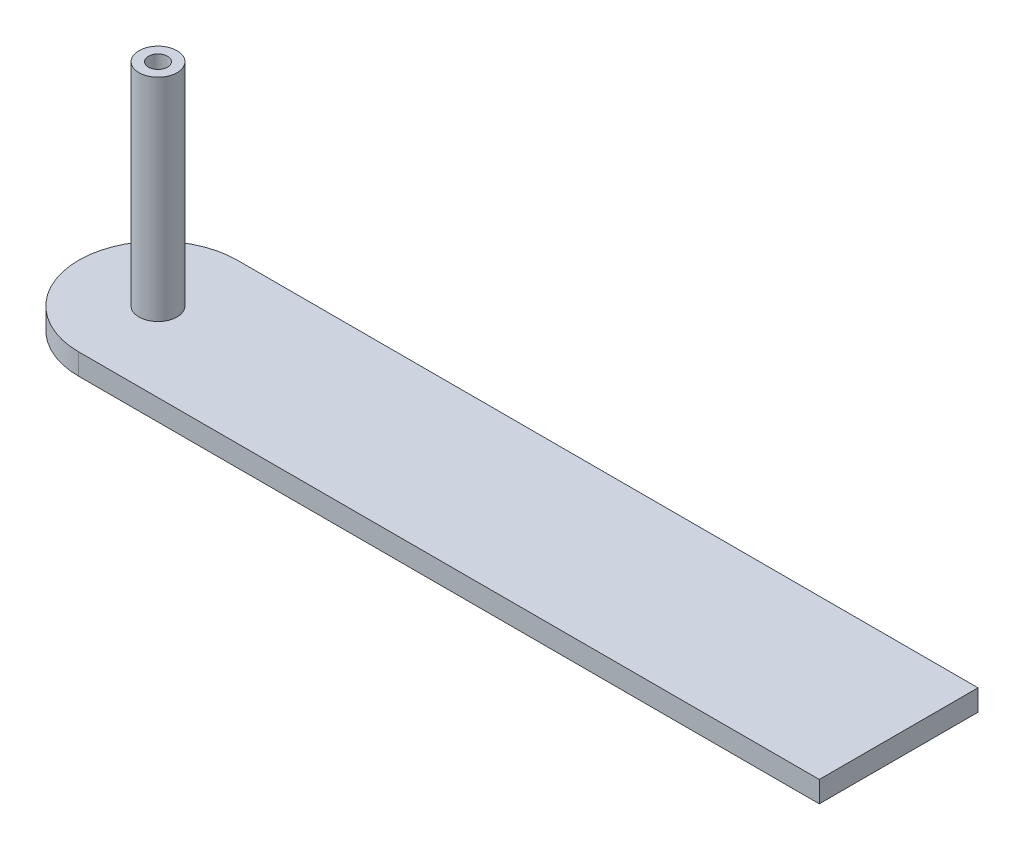
SolidWorks part; units mm, degrees
ref_plane "Front Plane" through (0, 0, 0) normal (0, 0, 1) x (1, 0, 0)
ref_plane "Top Plane" through (0, 0, 0) normal (0, 1, 0) x (1, 0, 0)
ref_plane "Right Plane" through (0, 0, 0) normal (1, 0, 0) x (0, 0, -1)
sketch "Sketch1" plane through (0, 0, 0) normal (0, 1, 0) x (1, 0, 0)
  line L1 (0, 0) -> (70, 0)
  line L2 (0, 0) -> (0, 15)
  line L3 (0, 15) -> (70, 15)
  line L4 (70, 0) -> (70, 15)
  dimension "D1" = 15
  dimension "D2" = 70
extrude "Boss-Extrude1" add sketch "Sketch1" along normal blind 2
sketch "Sketch2" plane through (0, 2, 0) normal (0, 1, 0) x (1, 0, 0)
  line L0 (0, 0) -> (0, 15) construction
  circle A0 centre (0, 7.5) radius 7.5
extrude "Boss-Extrude2" add sketch "Sketch2" along normal blind 2 from offset 2 offset against normal yes
sketch "Sketch3" plane through (0, 2, 0) normal (0, 1, 0) x (1, 0, 0)
  circle A0 centre (0, 7.5) radius 1.8
extrude "Boss-Extrude3" add sketch "Sketch3" along normal blind 20
sketch "Sketch6" plane through (0, 22, 0) normal (0, 1, 0) x (1, 0, 0)
  circle A0 centre (0, 7.5) radius 0.9
extrude "Cut-Extrude1" cut sketch "Sketch6" against normal blind 6.5
